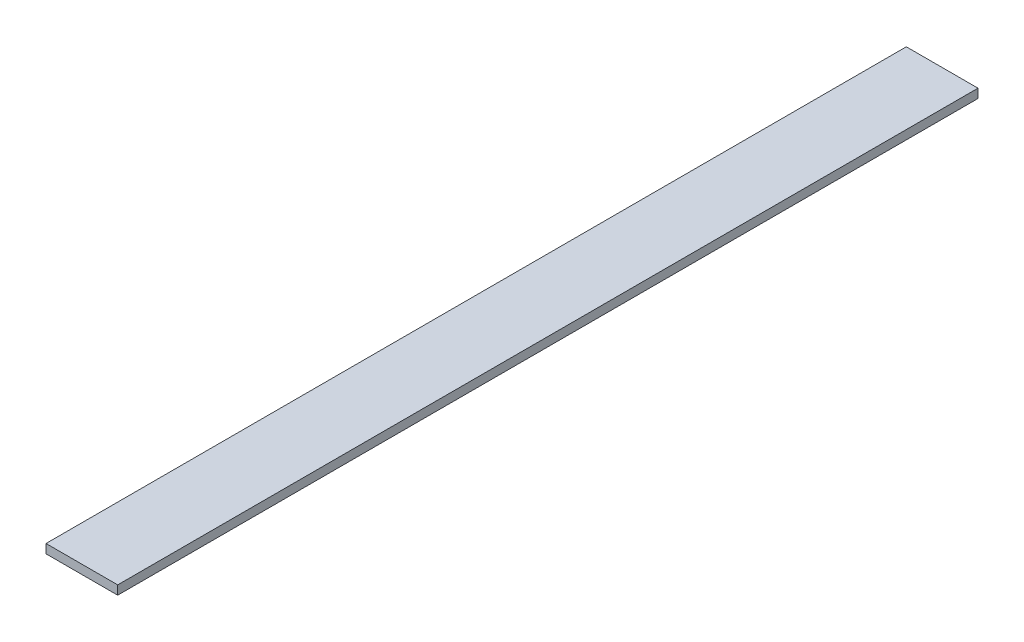
SolidWorks part; units mm, degrees
ref_plane "Front Plane" through (0, 0, 0) normal (0, 0, 1) x (1, 0, 0)
ref_plane "Top Plane" through (0, 0, 0) normal (0, 1, 0) x (1, 0, 0)
ref_plane "Right Plane" through (0, 0, 0) normal (1, 0, 0) x (0, 0, -1)
sketch "Sketch1" plane through (0, 0, 0) normal (0, 1, 0) x (1, 0, 0)
  line L1 (0, 0) -> (12.7, 0)
  line L2 (0, 0) -> (0, 152.4)
  line L3 (0, 152.4) -> (12.7, 152.4)
  line L4 (12.7, 0) -> (12.7, 152.4)
  dimension "D1" = 12.7
  dimension "D2" = 152.4
extrude "Boss-Extrude1" add sketch "Sketch1" along normal blind 1.5875
